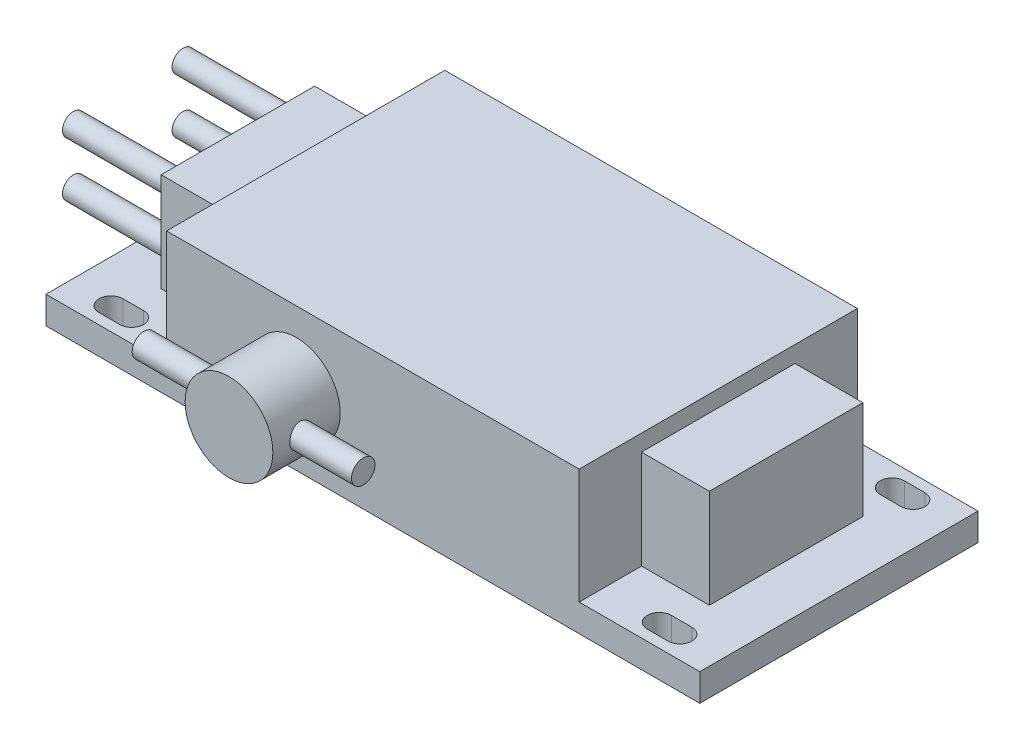
SolidWorks part; units mm, degrees
ref_plane "Спереди" through (0, 0, 0) normal (0, 0, 1) x (1, 0, 0)
ref_plane "Сверху" through (0, 0, 0) normal (0, 1, 0) x (1, 0, 0)
ref_plane "Справа" through (0, 0, 0) normal (1, 0, 0) x (0, 0, -1)
sketch "Sketch1" plane through (0, 0, 0) normal (0, 1, 0) x (1, 0, 0)
  line L0 (107.74, 21.25) -> (111.51, 21.25) construction
  line L1 (0, 25.375) -> (119.25, 25.375)
  line L2 (0, 25.375) -> (0, -25.375)
  line L3 (0, -25.375) -> (119.25, -25.375)
  line L4 (119.25, 25.375) -> (119.25, -25.375)
  line L5 (107.74, 23.435) -> (111.51, 23.435)
  line L6 (107.74, 19.065) -> (111.51, 19.065)
  line L7 (107.74, -21.25) -> (111.51, -21.25) construction
  line L8 (107.74, -19.065) -> (111.51, -19.065)
  line L9 (107.74, -23.435) -> (111.51, -23.435)
  line L10 (7.74, -21.25) -> (11.51, -21.25) construction
  line L11 (7.74, -19.065) -> (11.51, -19.065)
  line L12 (7.74, -23.435) -> (11.51, -23.435)
  line L13 (7.74, 21.25) -> (11.51, 21.25) construction
  line L14 (7.74, 23.435) -> (11.51, 23.435)
  line L15 (7.74, 19.065) -> (11.51, 19.065)
  line L16 (11.51, -21.25) -> (107.74, -21.25) construction
  line L17 (109.625, 21.25) -> (109.625, -21.25) construction
  arc A0 (107.74, 23.435) -> (107.74, 19.065) centre (107.74, 21.25) ccw
  arc A1 (111.51, 19.065) -> (111.51, 23.435) centre (111.51, 21.25) ccw
  arc A2 (107.74, -19.065) -> (107.74, -23.435) centre (107.74, -21.25) ccw
  arc A3 (111.51, -23.435) -> (111.51, -19.065) centre (111.51, -21.25) ccw
  arc A4 (7.74, -19.065) -> (7.74, -23.435) centre (7.74, -21.25) ccw
  arc A5 (11.51, -23.435) -> (11.51, -19.065) centre (11.51, -21.25) ccw
  arc A6 (7.74, 23.435) -> (7.74, 19.065) centre (7.74, 21.25) ccw
  arc A7 (11.51, 19.065) -> (11.51, 23.435) centre (11.51, 21.25) ccw
  point P5 (0, 0)
  point P8 (109.625, 21.25)
  point P13 (109.625, -21.25)
  point P20 (9.625, -21.25)
  point P27 (9.625, 21.25)
  point P36 (59.625, -21.25)
  point P37 (59.625, -25.375)
  point P38 (109.625, 0)
  point P39 (119.25, 0)
  point P42 (5.555, 21.25)
  point P43 (13.695, 21.25)
  dimension "D1" = 119.25
  dimension "D2" = 50.75
  dimension "D3" = 100
  dimension "D4" = 42.5
  dimension "D5" = 4.37
  dimension "D6" = 8.14
extrude "Extrude1" add sketch "Sketch1" along normal blind 5
sketch "Sketch2" plane through (0, 5, 0) normal (0, 1, 0) x (1, 0, 0)
  line L0 (119.25, 25.375) -> (0, 25.375) construction
  line L1 (22, 25.375) -> (97.25, 25.375)
  line L2 (22, 25.375) -> (22, -25.375)
  line L3 (22, -25.375) -> (97.25, -25.375)
  line L4 (97.25, 25.375) -> (97.25, -25.375)
  line L5 (0, -25.375) -> (119.25, -25.375) construction
  line L6 (0, 0) -> (119.25, 0) construction
  line L7 (119.25, -25.375) -> (119.25, 25.375) construction
  line L9 (22, -25.375) -> (97.25, 25.375) construction
  point P14 (59.625, 0)
  point P15 (59.625, 0)
  dimension "D1" = 22
extrude "Extrude2" add sketch "Sketch2" along normal blind 21
sketch "Sketch3" plane through (0, 5, 0) normal (0, 1, 0) x (1, 0, 0)
  line L0 (97.25, 25.375) -> (22, -25.375) construction
  line L1 (109.625, -14) -> (9.625, -14)
  line L2 (109.625, -14) -> (109.625, 14)
  line L3 (109.625, 14) -> (9.625, 14)
  line L4 (9.625, -14) -> (9.625, 14)
  line L5 (109.625, -14) -> (9.625, 14) construction
  point P9 (59.625, 0)
  point P10 (59.625, 0)
  dimension "D1" = 100
  dimension "D2" = 28
extrude "Extrude3" add sketch "Sketch3" along normal blind 18
sketch "Sketch4" plane through (0, 0, 25.375) normal (0, 0, 1) x (1, 0, 0)
  line L0 (45.6774, 0) -> (45.6774, 26) construction
  line L1 (0, 0) -> (119.25, 0) construction
  line L2 (22, 26) -> (97.25, 26) construction
  circle A0 centre (45.6774, 13) radius 8
  point P9 (45.6774, 13)
  dimension "D1" = 16
extrude "Extrude4" add sketch "Sketch4" along normal blind 12.3
sketch "Sketch5" plane through (97.25, 0, 0) normal (1, 0, 0) x (0, 0, -1)
  line L0 (-36.0689, 21) -> (-36.0689, 5) construction
  line L1 (-25.375, 21) -> (-37.675, 21) construction
  line L2 (-37.675, 5) -> (-25.375, 5) construction
  circle A0 centre (-32.4388, 13) radius 2.1441
  point P8 (-36.0689, 13)
extrude "Extrude5" add sketch "Sketch5" along normal blind 20 and the other way blind 20 from offset 52.32 offset against normal yes
sketch "Sketch6" plane through (9.625, 0, 0) normal (-1, 0, 0) x (0, 0, 1)
  line L12 (-10, 9) -> (10, 9)
  line L13 (10, 9) -> (10, 19)
  line L14 (10, 19) -> (-10, 19)
  line L15 (-10, 19) -> (-10, 9)
  line L16 (-10, 9) -> (10, 9) construction
  line L17 (10, 9) -> (10, 19) construction
  line L18 (10, 19) -> (-10, 19) construction
  line L19 (-10, 19) -> (-10, 9) construction
  circle A0 centre (-10, 9) radius 2
  circle A1 centre (-10, 19) radius 2
  circle A2 centre (10, 9) radius 2
  circle A3 centre (10, 19) radius 2
  dimension "D2" = 4
  dimension "D1" = 4
extrude "Extrude6" add sketch "Sketch6" along normal blind 20
ref_plane "Plane1" through (59.625, 0, 0) normal (1, 0, 0) x (0, 0, -1)
